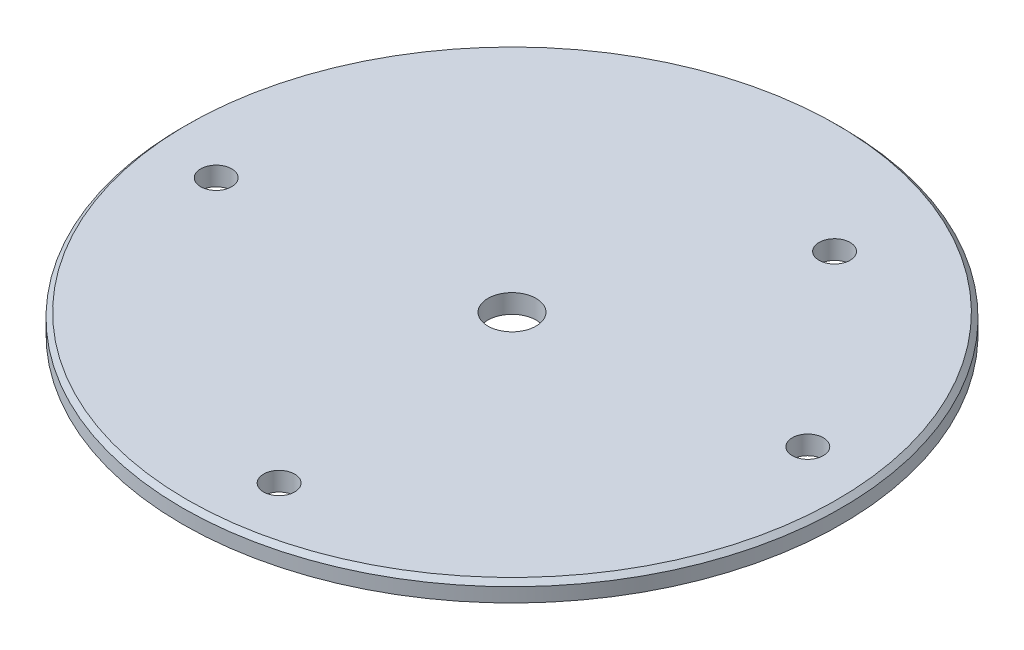
SolidWorks part; units mm, degrees
ref_plane "Front Plane" through (0, 0, 0) normal (0, 0, 1) x (1, 0, 0)
ref_plane "Top Plane" through (0, 0, 0) normal (0, 1, 0) x (1, 0, 0)
ref_plane "Right Plane" through (0, 0, 0) normal (1, 0, 0) x (0, 0, -1)
sketch "Sketch1" plane through (0, 0, 0) normal (0, 1, 0) x (1, 0, 0)
  circle A0 centre (0, 0) radius 35.015
  circle A1 centre (0, 0) radius 2.555
  dimension "D1" = 70.03
  dimension "D2" = 5.11
extrude "Boss-Extrude1" add sketch "Sketch1" along normal blind 2
chamfer "Chamfer1" distance 0.5 angle 45 1 edges at (0, 2, 35.015)
sketch "Sketch2" plane through (0, 2, 0) normal (0, 1, 0) x (1, 0, 0)
  circle A0 centre (28.0861, 3.3426) radius 2.15 construction
  circle A1 centre (11.5361, 22.7359) radius 2.15 construction
  circle A2 centre (-28.0861, -3.3426) radius 2.15 construction
  circle A3 centre (3.3426, -28.0861) radius 2.15 construction
  circle A4 centre (28.0861, 3.3426) radius 2.15 construction
  circle A5 centre (11.5361, 22.7359) radius 2.15 construction
  circle A6 centre (-28.0861, -3.3426) radius 2.15 construction
  circle A7 centre (3.3426, -28.0861) radius 2.15 construction
  point P13 (-28.0861, -3.3426)
  point P14 (3.3426, -28.0861)
  point P15 (28.0861, 3.3426)
  point P16 (11.5361, 22.7359)
hole_wizard "M4x0.7 Tapped Hole1" positions "3DSketch1" profile "Sketch3" tap size "M4x0.7" standard "ANSI Metric" end condition through all
sketch3d "3DSketch1"
  point P0 (3.3426, 2, 28.0861)
  point P3 (-28.0861, 2, 3.3426)
  point P6 (11.5361, 2, -22.7359)
  point P9 (28.0861, 2, -3.3426)
sketch "Sketch3" plane through (3.3426, 2, 28.0861) normal (1, 0, 0) x (0, 0, 1)
  line L0 (0, 0) -> (0, 2)
  line L1 (0, 2) -> (1.65, 2)
  line L2 (1.65, 2) -> (1.65, 0)
  line L5 (1.65, 0) -> (0, 0)
  line L11 (0, -6.35) -> (0, 107.95) construction
  dimension "Thru Tap Drill Dia." = 3.3
  dimension "Thru Tap Drill Depth" = 2
cosmetic thread "Hole Thread1" parameters "D2"=4
cosmetic thread "Hole Thread2" parameters "D2"=4
cosmetic thread "Hole Thread3" parameters "D2"=4
cosmetic thread "Hole Thread4" parameters "D2"=4
